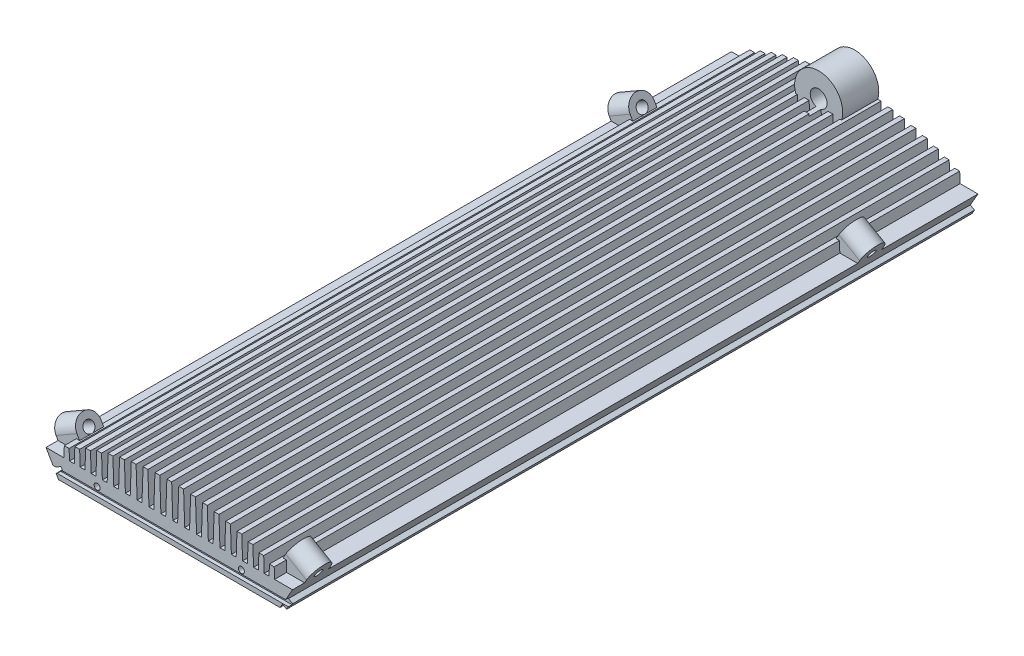
SolidWorks part; units mm, degrees
ref_plane "Plano frontal" through (0, 0, 0) normal (0, 0, 1) x (1, 0, 0)
ref_plane "Plano superior" through (0, 0, 0) normal (0, 1, 0) x (1, 0, 0)
ref_plane "Plano direito" through (0, 0, 0) normal (1, 0, 0) x (0, 0, -1)
sketch "Esboço1" plane through (0, 0, 0) normal (0, 0, 1) x (1, 0, 0)
  line L4 (0, 0) -> (-51.25, 88.7676) construction
  line L6 (-46.0538, 79.7676) -> (-51.25, 88.7676)
  line L7 (-51.25, 88.7676) -> (-43.7939, 88.7676)
  line L8 (-43.7939, 88.7676) -> (-43.6387, 93.2105)
  line L9 (-43.6387, 93.2105) -> (-41.6387, 93.2105)
  line L10 (-41.6387, 93.2105) -> (-41.4836, 88.7676)
  line L11 (-41.4836, 88.7676) -> (-39.4836, 88.7676)
  line L12 (-39.4836, 88.7676) -> (-39.2628, 95.0905)
  line L13 (-39.2628, 95.0905) -> (-37.2628, 95.0905)
  line L14 (-37.2628, 95.0905) -> (-37.042, 88.7676)
  line L15 (-37.042, 88.7676) -> (-35.042, 88.7676)
  line L16 (-35.042, 88.7676) -> (-34.7622, 96.78)
  line L17 (-34.7622, 96.78) -> (-32.7622, 96.78)
  line L18 (-32.7622, 96.78) -> (-32.4824, 88.7676)
  line L19 (-32.4824, 88.7676) -> (-30.4824, 88.7676)
  line L20 (-30.4824, 88.7676) -> (-30.1506, 98.2675)
  line L21 (-30.1506, 98.2675) -> (-28.1506, 98.2675)
  line L22 (-28.1506, 98.2675) -> (-27.8189, 88.7676)
  line L23 (-27.8189, 88.7676) -> (-25.8189, 88.7676)
  line L24 (-25.8189, 88.7676) -> (-25.4426, 99.543)
  line L25 (-25.4426, 99.543) -> (-23.4426, 99.543)
  line L26 (-23.4426, 99.543) -> (-23.0663, 88.7676)
  line L27 (-23.0663, 88.7676) -> (-21.0663, 88.7676)
  line L28 (-21.0663, 88.7676) -> (-20.6532, 100.5982)
  line L29 (-20.6532, 100.5982) -> (-18.6532, 100.5982)
  line L30 (-18.6532, 100.5982) -> (-18.24, 88.7676)
  line L31 (-18.24, 88.7676) -> (-16.24, 88.7676)
  line L32 (-16.24, 88.7676) -> (-15.798, 101.4262)
  line L33 (-15.798, 101.4262) -> (-13.798, 101.4262)
  line L34 (-13.798, 101.4262) -> (-13.3559, 88.7676)
  line L35 (1.4795, 88.7676) -> (1, 102.5)
  line L36 (3.4795, 88.7676) -> (1.4795, 88.7676)
  line L37 (-13.3559, 88.7676) -> (-11.3559, 88.7676)
  line L38 (-11.3559, 88.7676) -> (-10.8931, 102.0215)
  line L39 (-10.8931, 102.0215) -> (-8.8931, 102.0215)
  line L40 (-8.8931, 102.0215) -> (-8.4303, 88.7676)
  line L41 (3.9549, 102.3802) -> (3.4795, 88.7676)
  line L42 (-8.4303, 88.7676) -> (-6.4303, 88.7676)
  line L43 (-6.4303, 88.7676) -> (-5.9549, 102.3802)
  line L44 (-5.9549, 102.3802) -> (-3.9549, 102.3802)
  line L45 (-3.9549, 102.3802) -> (-3.4795, 88.7676)
  line L46 (-3.4795, 88.7676) -> (-1.4795, 88.7676)
  line L47 (-1.4795, 88.7676) -> (-1, 102.5)
  line L49 (5.9549, 102.3802) -> (3.9549, 102.3802)
  line L50 (0, 0) -> (0, 102.5) construction
  line L90 (0, 0) -> (-140.069, 0) construction
  line L91 (-46.0538, 79.7676) -> (46.0538, 79.7676)
  line L92 (-1, 102.5) -> (1, 102.5)
  line L93 (6.4303, 88.7676) -> (5.9549, 102.3802)
  line L94 (8.4303, 88.7676) -> (6.4303, 88.7676)
  line L95 (8.8931, 102.0215) -> (8.4303, 88.7676)
  line L96 (10.8931, 102.0215) -> (8.8931, 102.0215)
  line L97 (11.3559, 88.7676) -> (10.8931, 102.0215)
  line L98 (13.3559, 88.7676) -> (11.3559, 88.7676)
  line L99 (13.798, 101.4262) -> (13.3559, 88.7676)
  line L100 (15.798, 101.4262) -> (13.798, 101.4262)
  line L101 (16.24, 88.7676) -> (15.798, 101.4262)
  line L102 (18.24, 88.7676) -> (16.24, 88.7676)
  line L103 (18.6532, 100.5982) -> (18.24, 88.7676)
  line L104 (20.6532, 100.5982) -> (18.6532, 100.5982)
  line L105 (21.0663, 88.7676) -> (20.6532, 100.5982)
  line L106 (23.0663, 88.7676) -> (21.0663, 88.7676)
  line L107 (23.4426, 99.543) -> (23.0663, 88.7676)
  line L108 (25.4426, 99.543) -> (23.4426, 99.543)
  line L109 (25.8189, 88.7676) -> (25.4426, 99.543)
  line L110 (27.8189, 88.7676) -> (25.8189, 88.7676)
  line L111 (28.1506, 98.2675) -> (27.8189, 88.7676)
  line L112 (30.1506, 98.2675) -> (28.1506, 98.2675)
  line L113 (30.4824, 88.7676) -> (30.1506, 98.2675)
  line L114 (32.4824, 88.7676) -> (30.4824, 88.7676)
  line L115 (32.7622, 96.78) -> (32.4824, 88.7676)
  line L116 (34.7622, 96.78) -> (32.7622, 96.78)
  line L117 (35.042, 88.7676) -> (34.7622, 96.78)
  line L118 (37.042, 88.7676) -> (35.042, 88.7676)
  line L119 (37.2628, 95.0905) -> (37.042, 88.7676)
  line L120 (39.2628, 95.0905) -> (37.2628, 95.0905)
  line L121 (39.4836, 88.7676) -> (39.2628, 95.0905)
  line L122 (41.4836, 88.7676) -> (39.4836, 88.7676)
  line L123 (41.6387, 93.2105) -> (41.4836, 88.7676)
  line L124 (43.6387, 93.2105) -> (41.6387, 93.2105)
  line L125 (43.7939, 88.7676) -> (43.6387, 93.2105)
  line L126 (51.25, 88.7676) -> (43.7939, 88.7676)
  line L127 (46.0538, 79.7676) -> (51.25, 88.7676)
  circle A0 centre (0, 0) radius 102.5 construction
  point P4 (-42.6387, 93.2105)
  point P5 (-38.2628, 95.0905)
  point P6 (-33.7622, 96.78)
  point P9 (-29.1506, 98.2675)
  point P19 (0, 79.7676)
  point P68 (-24.4426, 99.543)
  point P69 (-19.6532, 100.5982)
  point P70 (-14.798, 101.4262)
  point P71 (-9.8931, 102.0215)
  point P80 (-4.9549, 102.3802)
  dimension "D1" = 205
  dimension "D2" = 9
  dimension "D3" = 60
  dimension "D4" = 2
  dimension "D5" = 1
  dimension "D6" = 92
  dimension "D7" = 92
  dimension "D8" = 2
extrude "Ressalto-extrusão1" add sketch "Esboço1" along normal blind 285
sketch "Esboço2" plane through (0, 0, 285) normal (0, 0, 1) x (1, 0, 0)
  line L0 (-47.0538, 81.4997) -> (-44.0228, 83.2497)
  line L2 (-44.0228, 83.2497) -> (-45.0228, 84.9817)
  line L5 (-48.0538, 83.2317) -> (-45.0228, 84.9817)
  line L6 (-48.0538, 83.2317) -> (-47.0538, 81.4997)
  line L7 (-51.25, 88.7676) -> (-46.0538, 79.7676) construction
  dimension "D1" = 2
  dimension "D2" = 3.5
  dimension "D3" = 2
extrude "Corte-extrusão1" cut sketch "Esboço2" against normal through all
sketch "Esboço3" plane through (0, 0, 285) normal (0, 0, 1) x (1, 0, 0)
  line L1 (46.0538, 79.7676) -> (51.25, 88.7676) construction
  line L6 (47.0538, 81.4997) -> (48.0538, 83.2317)
  line L10 (48.0538, 83.2317) -> (49.7859, 82.2317)
  line L11 (49.7859, 82.2317) -> (48.7859, 80.4997)
  line L12 (48.7859, 80.4997) -> (47.0538, 81.4997)
  dimension "D1" = 2
  dimension "D2" = 2
  dimension "D3" = 2
extrude "Ressalto-extrusão3" add sketch "Esboço3" against normal blind 285 separate body
sketch "Esboço13" plane through (0, 0, 0) normal (1, 0, 0) x (0, 0, -1)
  line L0 (-285, 83.7676) -> (-283.5, 83.7676)
  line L1 (-283.5, 83.7676) -> (-283.5, 81.7676)
  line L2 (-283.5, 81.7676) -> (-285, 81.7676)
  line L3 (-285, 81.7676) -> (-285, 83.7676)
  line L4 (-285, 79.7676) -> (0, 79.7676) construction
  line L5 (-285, 84.9817) -> (-285, 83.2317) construction
  dimension "D1" = 2
  dimension "D2" = 2
  dimension "D3" = 1.5
extrude "Corte-extrusão7" cut sketch "Esboço13" against normal through all both and the other way through all
sketch "Esboço5" plane through (0, 0, 285) normal (0, 0, 1) x (1, 0, 0)
  line L0 (-46.0538, 79.7676) -> (46.0538, 79.7676) construction
  circle A0 centre (-30, 85.2676) radius 1.25
  circle A1 centre (30, 85.2676) radius 1.25
  dimension "D1" = 2.5
  dimension "D2" = 21.25
  dimension "D3" = 5.5
  dimension "D4" = 2.5
  dimension "D5" = 21.25
  dimension "D6" = 5.5
extrude "Corte-extrusão3" cut sketch "Esboço5" against normal blind 10
sketch "Esboço6" plane through (0, 0, 0) normal (-0.866, -0.5, 0) x (0, 0, 1)
  line L0 (280, 104.1077) -> (280, 96.292)
  line L1 (280, 96.292) -> (270, 96.292)
  line L2 (270, 96.292) -> (270, 104.1077)
  line L3 (285, 102.5) -> (285, 96.7265) construction
  line L4 (285, 102.542) -> (0, 102.542) construction
  line L6 (0, 96.1077) -> (283.5, 96.1077) construction
  arc A0 (270, 104.1077) -> (280, 104.1077) centre (275, 104.1077) cw
  line M5 (285, 102.5) -> (0, 102.5)
  dimension "D2" = 5
  dimension "D1" = 5
  dimension "D3" = 10
  dimension "D4" = 6.25
  dimension "D5" = 8
extrude "Ressalto-extrusão4" add sketch "Esboço6" against normal blind 10 contours A0 L2 L0 M5 | L2 L1 L0 M5
sketch "Esboço7" plane through (0, 0, 0) normal (-0.866, -0.5, 0) x (0, 0, 1)
  circle A0 centre (275, 104.1077) radius 2.25
  dimension "D1" = 4.5
extrude "Corte-extrusão4" cut sketch "Esboço7" against normal blind 10
sketch "Esboço8" plane through (0, 0, 0) normal (0.866, -0.5, 0) x (0, 0, -1)
  line L0 (-280, 104.1077) -> (-280, 96.1077)
  line L1 (-280, 96.1077) -> (-270, 96.1077)
  line L2 (-270, 96.1077) -> (-270, 104.1077)
  line L3 (-285, 96.7265) -> (-285, 102.5) construction
  line L4 (0, 96.1077) -> (-283.5, 96.1077) construction
  line L5 (0, 96.1077) -> (-283.5, 96.1077) construction
  arc A0 (-280, 104.1077) -> (-270, 104.1077) centre (-275, 104.1077) cw
  dimension "D1" = 5
  dimension "D4" = 8
  dimension "D2" = 10
  dimension "D3" = 5
  dimension "D5" = 8
  dimension "D6" = 8
extrude "Ressalto-extrusão5" add sketch "Esboço8" against normal blind 10
sketch "Esboço9" plane through (0, 0, 0) normal (0.866, -0.5, 0) x (0, 0, -1)
  circle A0 centre (-275, 104.1077) radius 1.65
  dimension "D1" = 3.3
extrude "Corte-extrusão5" cut sketch "Esboço9" against normal blind 10
pattern_linear "Padrão linear1" count 2 spacing 230 along (0, 0, -1) of "Ressalto-extrusão4", "Corte-extrusão4", "Ressalto-extrusão5", "Corte-extrusão5"
sketch "Esboço10" plane through (0, 0, 0) normal (0, 0, -1) x (-1, 0, 0)
  line L0 (10.8931, 102.0215) -> (10.8931, 84.6005)
  line L2 (10.8931, 84.6005) -> (-10.8931, 84.6005)
  line L3 (-10.8931, 84.6005) -> (-10.8931, 102.0215)
  line L5 (-10.8931, 102.0215) -> (-9.5461, 102.0215)
  line L7 (10.8931, 102.0215) -> (9.5461, 102.0215)
  line L8 (46.0538, 79.7676) -> (-46.0538, 79.7676) construction
  line L9 (0, 12.5028) -> (0, -12.5028) construction
  arc A1 (9.5461, 102.0215) -> (-9.5461, 102.0215) centre (0, 105) ccw
  dimension "D1" = 10
  dimension "D3" = 25.2324
extrude "Ressalto-extrusão6" add sketch "Esboço10" against normal blind 15 contours L7 A1 L5 L3 L2 L0
sketch "Esboço12" plane through (0, 0, 0) normal (0, 0, -1) x (-1, 0, 0)
  circle A0 centre (0, 105) radius 3.5
  dimension "D1" = 7
extrude "Corte-extrusão6" cut sketch "Esboço12" against normal blind 20
sketch "Esboço14" plane through (0, 79.7676, 0) normal (0, -1, 0) x (-1, 0, 0)
  circle A0 centre (-36.5, -246.65) radius 1.65
  circle A1 centre (-21.254, -234.65) radius 1.25
  circle A2 centre (36.5, -246.65) radius 1.65
  circle A3 centre (22.307, -180.42) radius 1.25
  circle A4 centre (38.5, -26.15) radius 1.65
  circle A5 centre (15.449, -26.242) radius 1.25
  circle A6 centre (15.83, -8.335) radius 1.25
  circle A7 centre (-32.5, -12.65) radius 1.65
  circle A8 centre (-25.572, -49.15) radius 1.25
  circle A9 centre (-21.762, -76.661) radius 1.25
  circle A10 centre (25.863, -97.743) radius 1.25
  circle A11 centre (-27.096, -173.943) radius 1.25
  circle A12 centre (-38.145, -142.066) radius 1.65
  circle A13 centre (-17.5, -217.65) radius 1.25
  circle A14 centre (-17.5, -197.65) radius 1.25
  circle A15 centre (-17.5, -177.65) radius 1.25
  circle A16 centre (-17.5, -157.65) radius 1.25
  circle A17 centre (17.5, -127.65) radius 1.25
  circle A18 centre (17.5, -107.65) radius 1.25
  circle A19 centre (17.5, -87.65) radius 1.25
  circle A20 centre (17.5, -67.65) radius 1.25
  dimension "D1" = 3.3
  dimension "D2" = 2.5
extrude "Corte-extrusão8" cut sketch "Esboço14" against normal blind 8
